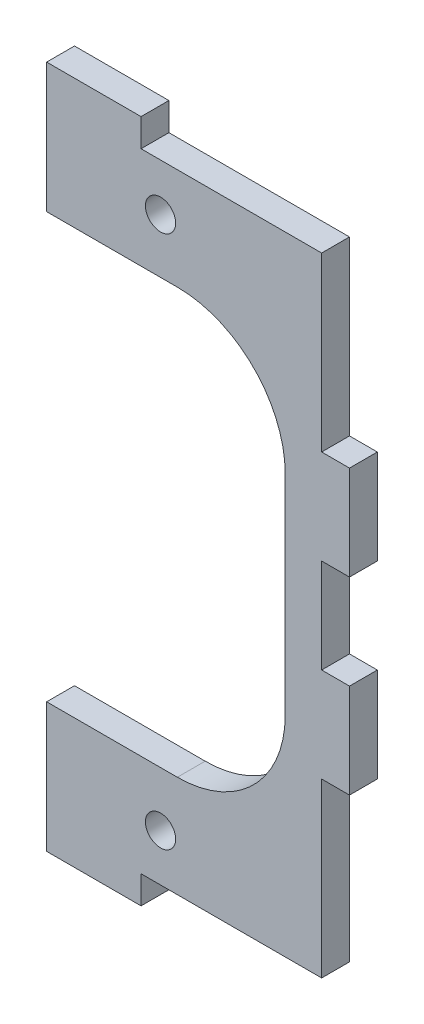
SolidWorks part; units mm, degrees
ref_plane "Front Plane" through (0, 0, 0) normal (0, 0, 1) x (1, 0, 0)
ref_plane "Top Plane" through (0, 0, 0) normal (0, 1, 0) x (1, 0, 0)
ref_plane "Right Plane" through (0, 0, 0) normal (1, 0, 0) x (0, 0, -1)
sketch "Sketch1" plane through (0, 0, 0) normal (0, 0, 1) x (1, 0, 0)
  line L0 (-12.065, 21.746) -> (-12.065, -88.254) construction
  line L1 (-12.065, 2.95) -> (-12.065, -69.458)
  line L2 (17.065, 21.746) -> (17.065, -88.254) construction
  line L3 (17.065, 0) -> (17.065, -66.508)
  line L5 (-12.065, 0) -> (17.065, 0)
  line L6 (-12.065, 0) -> (-12.065, -66.508)
  line L7 (-12.065, -66.508) -> (17.065, -66.508)
  line L8 (-2.065, 2.95) -> (-15.015, 2.95)
  line L9 (-15.015, 2.95) -> (-15.015, 0)
  line L10 (-15.015, 0) -> (-2.065, 0)
  line L11 (-2.065, 0) -> (-2.065, 2.95)
  line L12 (-2.065, 2.95) -> (-12.065, 2.95)
  line L14 (-12.065, 0) -> (-2.065, 0)
  line L15 (-2.065, 0) -> (-2.065, 2.95)
  line L16 (-2.065, -66.508) -> (-15.015, -66.508)
  line L17 (-15.015, -66.508) -> (-15.015, -69.458)
  line L18 (-15.015, -69.458) -> (-2.065, -69.458)
  line L19 (-2.065, -69.458) -> (-2.065, -66.508)
  line L20 (-2.065, -66.508) -> (-12.065, -66.508)
  line L22 (-12.065, -69.458) -> (-2.065, -69.458)
  line L23 (-2.065, -69.458) -> (-2.065, -66.508)
  line L24 (17.065, 0) -> (17.065, -66.508)
  line L25 (-12.065, 0) -> (17.065, -66.508) construction
  line L26 (-12.065, -66.508) -> (17.065, 0) construction
  point P16 (2.5, -33.254)
  dimension "D1" = 0
  dimension "D2" = 0
extrude "Boss-Extrude1" add sketch "Sketch1" along normal up to surface (2.95 mm away) contours L1 L7 L3 L5 | L5 L15 L12 L1 | L22 L23 L7 L1
sketch "Sketch2" plane through (0, 0, 2.95) normal (0, 0, 1) x (1, 0, 0)
  line L0 (17.065, 0) -> (-12.065, -66.508)
  line L2 (-12.065, -10.7738) -> (13.208, -10.7738)
  line L3 (-12.065, -10.7738) -> (-12.065, -55.7342)
  line L4 (-12.065, -55.7342) -> (13.208, -55.7342)
  line L5 (13.208, -10.7738) -> (13.208, -55.7342)
  line L6 (-12.065, -10.7738) -> (13.208, -55.7342) construction
  line L7 (-12.065, -55.7342) -> (13.208, -10.7738) construction
  line L8 (-2.065, 2.95) -> (-12.065, 2.95)
  line L9 (-12.065, 2.95) -> (-12.065, -69.458)
  line L10 (-12.065, -69.458) -> (-2.065, -69.458)
  line L11 (-2.065, -69.458) -> (-2.065, -66.508)
  line L12 (-2.065, -66.508) -> (17.065, -66.508)
  line L13 (17.065, -66.508) -> (17.065, 0)
  line L14 (17.065, 0) -> (-2.065, 0)
  line L15 (-2.065, 0) -> (-2.065, 2.95)
  line L16 (-2.065, 2.95) -> (-12.065, 2.95)
  line L17 (-12.065, 2.95) -> (-12.065, -69.458)
  line L18 (-12.065, -69.458) -> (-2.065, -69.458)
  line L19 (-2.065, -69.458) -> (-2.065, -66.508)
  line L20 (-2.065, -66.508) -> (17.065, -66.508)
  line L21 (17.065, -66.508) -> (17.065, 0)
  line L22 (17.065, 0) -> (-2.065, 0)
  line L23 (-2.065, 0) -> (-2.065, 2.95)
  point P14 (0.5715, -33.254)
  point P15 (2.5, -33.254)
  line M14 (-12.065, 2.95) -> (-12.065, -69.458)
  dimension "D2" = 25.273
  dimension "D3" = 44.9605
  dimension "D1" = 0
extrude "Cut-Extrude1" cut sketch "Sketch2" against normal through all contours L5 L2 L0 L4 | L4 L0 L2 M14
fillet "Fillet1" radius 11.43 2 edges at (13.208, -10.7738, 1.475) (13.208, -55.7342, 1.475)
sketch "Sketch3" plane through (0, 0, 2.95) normal (0, 0, 1) x (1, 0, 0)
  line L1 (17.065, -38.254) -> (17.065, -28.254)
  line L2 (17.065, -18.254) -> (12.5039, -18.254)
  line L3 (17.065, -48.254) -> (12.5039, -48.254)
  line L12 (-12.065, -55.7342) -> (-12.065, -69.458)
  line L13 (1.778, -55.7342) -> (-12.065, -55.7342)
  line L14 (13.208, -22.2038) -> (13.208, -44.3042)
  line L15 (-12.065, -10.7738) -> (1.778, -10.7738)
  line L16 (-12.065, 2.95) -> (-12.065, -10.7738)
  line L17 (-2.065, 2.95) -> (-12.065, 2.95)
  line L18 (-2.065, 0) -> (-2.065, 2.95)
  line L19 (17.065, 0) -> (-2.065, 0)
  line L20 (17.065, -66.508) -> (17.065, 0)
  line L21 (-2.065, -66.508) -> (17.065, -66.508)
  line L22 (-2.065, -69.458) -> (-2.065, -66.508)
  line L23 (-12.065, -69.458) -> (-2.065, -69.458)
  line L26 (13.208, -22.2038) -> (13.208, -44.3042)
  line L68 (0, -69.458) -> (-12.065, -69.458)
  line L69 (-12.065, -69.458) -> (-12.065, -80.529)
  line L82 (-12.065, -88.254) -> (17.065, -88.254)
  line L83 (17.065, -88.254) -> (17.065, -68.254)
  line L84 (17.065, -68.254) -> (20.015, -68.254)
  line L85 (20.015, -68.254) -> (20.015, -58.254)
  line L86 (20.015, -58.254) -> (17.065, -58.254)
  line L87 (17.065, -58.254) -> (17.065, -48.254)
  line L88 (17.065, -48.254) -> (20.015, -48.254)
  line L89 (20.015, -48.254) -> (20.015, -38.254)
  line L90 (20.015, -38.254) -> (17.065, -38.254)
  line L91 (17.065, -38.254) -> (17.065, -28.254)
  line L92 (17.065, -28.254) -> (20.015, -28.254)
  line L93 (20.015, -28.254) -> (20.015, -18.254)
  line L94 (20.015, -18.254) -> (17.065, -18.254)
  line L95 (17.065, -18.254) -> (17.065, -8.254)
  line L96 (17.065, -8.254) -> (20.015, -8.254)
  line L97 (20.015, -8.254) -> (20.015, 1.746)
  line L98 (20.015, 1.746) -> (17.065, 1.746)
  line L99 (17.065, 1.746) -> (17.065, 21.746)
  line L100 (17.065, 21.746) -> (-12.065, 21.746)
  line L101 (-12.065, 21.746) -> (-12.065, 17.221)
  line L114 (-12.065, 2.95) -> (0, 2.95)
  line L115 (0, 2.95) -> (0, 0)
  line L116 (0, 0) -> (-12.065, 0)
  line L117 (-12.065, 0) -> (-12.065, 1.746)
  line L118 (-12.065, 1.746) -> (-15.015, 1.746)
  line L119 (-15.015, 1.746) -> (-15.015, -8.254)
  line L120 (-15.015, -8.254) -> (-12.065, -8.254)
  line L121 (-12.065, -8.254) -> (-12.065, -18.254)
  line L122 (-12.065, -18.254) -> (-15.015, -18.254)
  line L123 (-15.015, -18.254) -> (-15.015, -28.254)
  line L124 (-15.015, -28.254) -> (-12.065, -28.254)
  line L125 (-12.065, -28.254) -> (-12.065, -38.254)
  line L126 (-12.065, -38.254) -> (-15.015, -38.254)
  line L127 (-15.015, -38.254) -> (-15.015, -48.254)
  line L128 (-15.015, -48.254) -> (-12.065, -48.254)
  line L129 (-12.065, -48.254) -> (-12.065, -58.254)
  line L130 (-12.065, -58.254) -> (-15.015, -58.254)
  line L131 (-15.015, -58.254) -> (-15.015, -68.254)
  line L132 (-15.015, -68.254) -> (-12.065, -68.254)
  line L133 (-12.065, -68.254) -> (-12.065, -66.508)
  line L134 (-12.065, -66.508) -> (0, -66.508)
  line L135 (0, -66.508) -> (0, -69.458)
  line L156 (17.065, -48.254) -> (20.015, -48.254)
  line L157 (20.015, -48.254) -> (20.015, -38.254)
  line L158 (20.015, -38.254) -> (17.065, -38.254)
  line L159 (17.065, -38.254) -> (17.065, -28.254)
  line L160 (17.065, -28.254) -> (20.015, -28.254)
  line L161 (20.015, -28.254) -> (20.015, -18.254)
  line L162 (20.015, -18.254) -> (17.065, -18.254)
  line L437 (-12.065, -80.529) -> (-7.315, -80.529)
  line L438 (-7.315, -80.529) -> (-7.315, -79.479)
  line L439 (-7.315, -79.479) -> (-5.015, -79.479)
  line L440 (-5.015, -79.479) -> (-5.015, -80.529)
  line L441 (-5.015, -80.529) -> (-3.015, -80.529)
  line L442 (-3.015, -80.529) -> (-3.015, -83.729)
  line L443 (-3.015, -83.729) -> (-5.015, -83.729)
  line L444 (-5.015, -83.729) -> (-5.015, -84.779)
  line L445 (-5.015, -84.779) -> (-7.315, -84.779)
  line L446 (-7.315, -84.779) -> (-7.315, -83.729)
  line L447 (-7.315, -83.729) -> (-12.065, -83.729)
  line L448 (-12.065, -83.729) -> (-12.065, -88.254)
  line L449 (-12.065, 17.221) -> (-7.315, 17.221)
  line L450 (-7.315, 17.221) -> (-7.315, 18.271)
  line L451 (-7.315, 18.271) -> (-5.015, 18.271)
  line L452 (-5.015, 18.271) -> (-5.015, 17.221)
  line L453 (-5.015, 17.221) -> (-3.015, 17.221)
  line L454 (-3.015, 17.221) -> (-3.015, 14.021)
  line L455 (-3.015, 14.021) -> (-5.015, 14.021)
  line L456 (-5.015, 14.021) -> (-5.015, 12.971)
  line L457 (-5.015, 12.971) -> (-7.315, 12.971)
  line L458 (-7.315, 12.971) -> (-7.315, 14.021)
  line L459 (-7.315, 14.021) -> (-12.065, 14.021)
  line L460 (-12.065, 14.021) -> (-12.065, 2.95)
  arc A2 (1.778, -55.7342) -> (13.208, -44.3042) centre (1.778, -44.3042) ccw
  arc A3 (13.208, -22.2038) -> (1.778, -10.7738) centre (1.778, -22.2038) ccw
  arc A4 (12.5039, -48.254) -> (13.208, -44.3042) centre (1.778, -44.3042) ccw
  arc A5 (13.208, -22.2038) -> (12.5039, -18.254) centre (1.778, -22.2038) ccw
  line M88 (17.065, -66.508) -> (17.065, 0)
  arc M94 (1.778, -10.7738) -> (13.208, -22.2038) centre (1.778, -22.2038) cw
  line M95 (13.208, -22.2038) -> (13.208, -44.3042)
  arc M96 (13.208, -44.3042) -> (1.778, -55.7342) centre (1.778, -44.3042) cw
  dimension "D1" = 0
  dimension "D2" = 0
extrude "Boss-Extrude2" add sketch "Sketch3" against normal up to surface (2.95 mm away) contours L3 L2 M88 M94 M95 M96 | L161 L162 L160 M88 | L157 L158 L156 M88 up to face at (0.8797, -33.254, 0)
sketch "Sketch4" plane through (0, 0, 2.95) normal (0, 0, 1) x (1, 0, 0)
  circle A0 centre (0, -61.508) radius 1.6 construction
  circle A1 centre (0, -5) radius 1.6 construction
  circle A2 centre (0, -61.508) radius 1.6
  circle A3 centre (0, -5) radius 1.6
extrude "Cut-Extrude2" cut sketch "Sketch4" against normal through all
equation "\"D2@Sketch2\"=.995in"
equation "\"D3@Sketch2\"=1.77in+1/16in"
